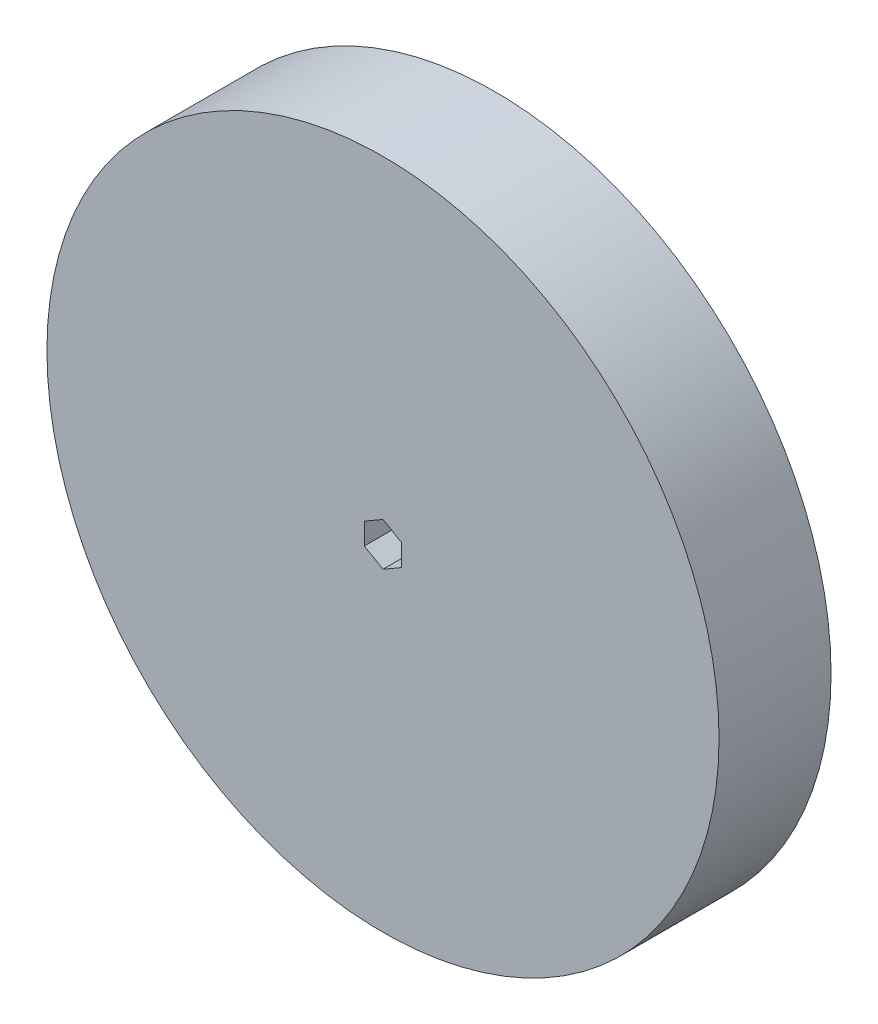
SolidWorks part; units mm, degrees
material "Silicon"
ref_plane "Front Plane" through (0, 0, 0) normal (0, 0, 1) x (1, 0, 0)
ref_plane "Top Plane" through (0, 0, 0) normal (0, 1, 0) x (1, 0, 0)
ref_plane "Right Plane" through (0, 0, 0) normal (1, 0, 0) x (0, 0, -1)
sketch "Sketch2" plane through (0, 0, 0) normal (0, 0, 1) x (1, 0, 0)
  circle A0 centre (0, 0) radius 57.15
  dimension "D1" = 114.3
extrude "Boss-Extrude1" add sketch "Sketch2" along normal blind 19.05
sketch "Sketch4" plane through (0, 0, 0) normal (0, 0, -1) x (-1, 0, 0)
  line L1 (0, 3.6662) -> (-3.175, 1.8331)
  line L2 (-3.175, 1.8331) -> (-3.175, -1.8331)
  line L3 (-3.175, -1.8331) -> (0, -3.6662)
  line L4 (0, -3.6662) -> (3.175, -1.8331)
  line L5 (3.175, -1.8331) -> (3.175, 1.8331)
  line L6 (3.175, 1.8331) -> (0, 3.6662)
  circle A0 centre (0, 0) radius 3.175 construction
  dimension "D1" = 6.35
extrude "Cut-Extrude1" cut sketch "Sketch4" against normal blind 19.05
